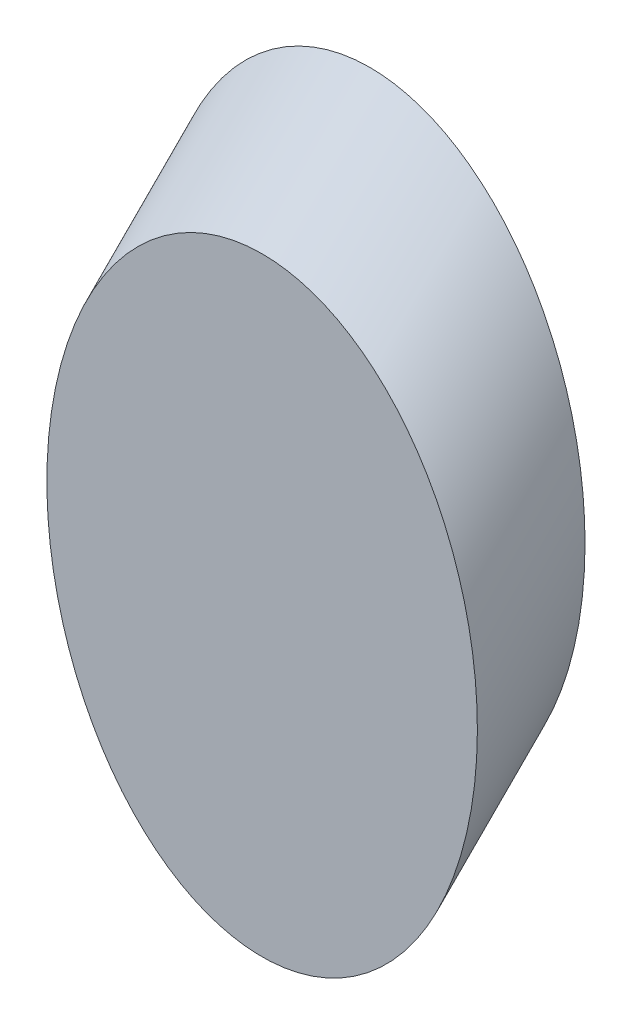
SolidWorks part; units mm, degrees
ref_plane "前视基准面" through (0, 0, 0) normal (0, 0, 1) x (1, 0, 0)
ref_plane "上视基准面" through (0, 0, 0) normal (0, 1, 0) x (1, 0, 0)
ref_plane "右视基准面" through (0, 0, 0) normal (1, 0, 0) x (0, 0, -1)
sketch "草图1" plane through (0, 0, 0) normal (0, 0, 1) x (1, 0, 0)
  ellipse E0 centre (54.3924, 35.7889) end of major axis (54.3924, 71.1489) minor radius 25
  dimension "D1" = 50
  dimension "D2" = 70.72
sketch3d "3D草图2"
  line L0 (55.1123, 71.1342, 0) -> (55.1123, 71.1342, -2.7888)
  line L3 (55.1123, 71.1342, 0) -> (55.1123, 44.6362, 26.498)
  line L4 (55.1123, 71.1342, 0) -> (55.1123, 28.9476, 0)
  spline S2 degree 3 poles (54.3924, 71.1489, 0) (4.3924, 71.1489, 0) (4.3924, 0.4289, 0) (54.3924, 0.4289, 0) (104.3924, 0.4289, 0) (104.3924, 71.1489, 0) (54.3924, 71.1489, 0) (4.3924, 71.1489, 0) (4.3924, 0.4289, 0) knots -0.5 0 0 0 0.5 0.5 0.5 1 1 1 1.5 1.5 1.5 weights 1 0.333333 0.333333 1 0.333333 0.333333 1 0.333333 0.333333 only from (54.3924, 71.1489, 0) to (54.3924, 71.1489, 0) construction
  dimension "D1" = 45
extrude "凸台-拉伸2" add sketch "草图1" along direction (0, -0.7071, 0.7071) on the side against the normal blind 17.68
